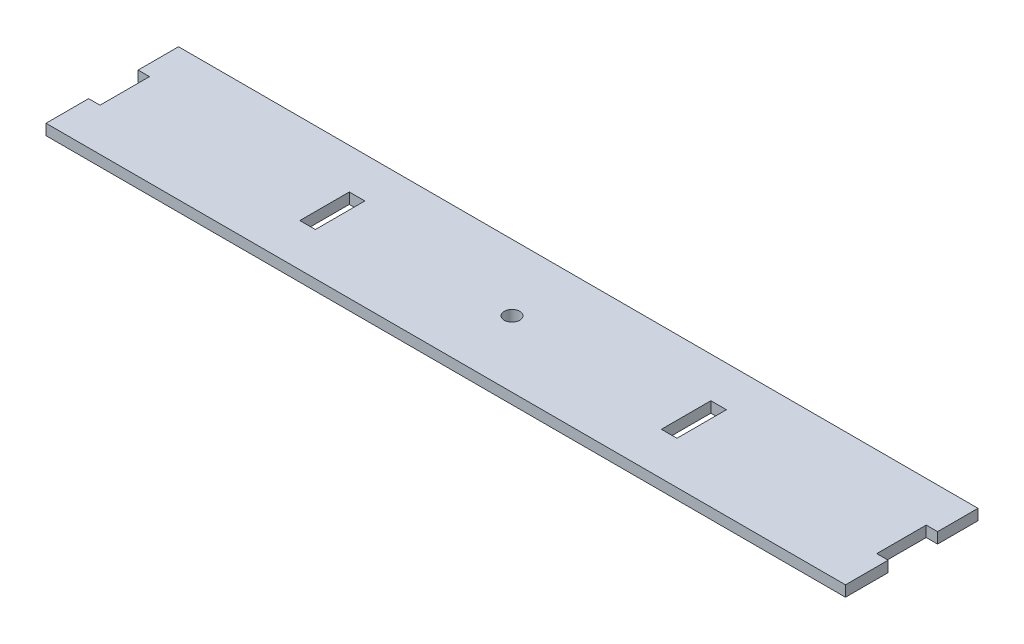
SolidWorks part; units mm, degrees
material "Plain Carbon Steel"
ref_plane "Front Plane" through (0, 0, 0) normal (0, 0, 1) x (1, 0, 0)
ref_plane "Top Plane" through (0, 0, 0) normal (0, 1, 0) x (1, 0, 0)
ref_plane "Right Plane" through (0, 0, 0) normal (1, 0, 0) x (0, 0, -1)
sketch "Sketch1" plane through (0, 0, 0) normal (0, 1, 0) x (1, 0, 0)
  line L0 (0, 29.21) -> (0, 0) construction
  line L1 (-177.8, 29.21) -> (177.8, 29.21)
  line L2 (-177.8, 29.21) -> (-177.8, -29.21)
  line L3 (-177.8, -29.21) -> (177.8, -29.21)
  line L4 (177.8, 29.21) -> (177.8, -29.21)
  line L5 (0, 0) -> (177.8, 0) construction
  dimension "D1" = 177.8
  dimension "D2" = 29.21
extrude "Boss-Extrude1" add sketch "Sketch1" along normal blind 4.7625
sketch "Sketch2" plane through (0, 0, 0) normal (0, -1, 0) x (-1, 0, 0)
  line L0 (177.8, 29.21) -> (177.8, -29.21) construction
  line L1 (171.45, -10.16) -> (177.8, -10.16)
  line L2 (171.45, -10.16) -> (171.45, 11.1389)
  line L3 (171.45, 11.1389) -> (177.8, 11.1389)
  line L4 (177.8, -10.16) -> (177.8, 11.1389)
  line L5 (171.45, 11.1389) -> (177.8, 11.1389) construction
  line L6 (-177.8, -29.21) -> (-177.8, 29.21) construction
  line L7 (82.55, -10.16) -> (76.2, -10.16)
  line L8 (82.55, -10.16) -> (82.55, 11.1389)
  line L9 (82.55, 11.1389) -> (76.2, 11.1389)
  line L10 (76.2, -10.16) -> (76.2, 11.1389)
  line L11 (-76.2, -10.16) -> (-82.55, -10.16)
  line L12 (-76.2, -10.16) -> (-76.2, 11.1389)
  line L13 (-76.2, 11.1389) -> (-82.55, 11.1389)
  line L14 (-82.55, -10.16) -> (-82.55, 11.1389)
  line L15 (-171.45, -10.16) -> (-177.8, -10.16)
  line L16 (-171.45, -10.16) -> (-171.45, 11.1389)
  line L17 (-171.45, 11.1389) -> (-177.8, 11.1389)
  line L18 (-177.8, -10.16) -> (-177.8, 11.1389)
  line L19 (-177.8, 11.1389) -> (-171.45, 11.1389) construction
  line L20 (171.196, -10.414) -> (171.196, 11.3929)
  line L21 (171.196, 11.3929) -> (178.054, 11.3929)
  line L22 (178.054, -10.414) -> (178.054, 11.3929)
  line L23 (171.196, -10.414) -> (178.054, -10.414)
  line L24 (75.946, -10.414) -> (75.946, 11.3929)
  line L25 (82.804, 11.3929) -> (75.946, 11.3929)
  line L26 (82.804, -10.414) -> (82.804, 11.3929)
  line L27 (82.804, -10.414) -> (75.946, -10.414)
  line L28 (-82.804, -10.414) -> (-82.804, 11.3929)
  line L29 (-75.946, 11.3929) -> (-82.804, 11.3929)
  line L30 (-75.946, -10.414) -> (-75.946, 11.3929)
  line L31 (-75.946, -10.414) -> (-82.804, -10.414)
  line L32 (-171.196, -10.414) -> (-171.196, 11.3929)
  line L33 (-171.196, 11.3929) -> (-178.054, 11.3929)
  line L34 (-178.054, -10.414) -> (-178.054, 11.3929)
  line L35 (-171.196, -10.414) -> (-178.054, -10.414)
  dimension "D1" = 0.254
extrude "Cut-Extrude1" cut sketch "Sketch2" against normal through all
sketch "Sketch3" plane through (0, 0, 0) normal (0, -1, 0) x (1, 0, 0)
  line L0 (176.2125, -29.21) -> (176.2125, 29.21)
  line L1 (-176.2125, 29.21) -> (-176.2125, -29.21)
  line L12 (171.196, -11.3929) -> (171.196, 10.414)
  line L13 (171.196, 10.414) -> (177.8, 10.414)
  line L14 (177.8, 10.414) -> (177.8, 29.21)
  line L15 (177.8, 29.21) -> (-177.8, 29.21)
  line L16 (-177.8, 29.21) -> (-177.8, 10.414)
  line L17 (-177.8, 10.414) -> (-171.196, 10.414)
  line L18 (-171.196, 10.414) -> (-171.196, -11.3929)
  line L19 (-171.196, -11.3929) -> (-177.8, -11.3929)
  line L20 (-177.8, -11.3929) -> (-177.8, -29.21)
  line L21 (-177.8, -29.21) -> (177.8, -29.21)
  line L22 (177.8, -29.21) -> (177.8, -11.3929)
  line L23 (177.8, -11.3929) -> (171.196, -11.3929)
  line L24 (171.196, -11.3929) -> (171.196, 10.414)
  line L25 (171.196, 10.414) -> (177.8, 10.414)
  line L26 (177.8, 10.414) -> (177.8, 29.21)
  line L27 (177.8, 29.21) -> (-177.8, 29.21)
  line L28 (-177.8, 29.21) -> (-177.8, 10.414)
  line L29 (-177.8, 10.414) -> (-171.196, 10.414)
  line L30 (-171.196, 10.414) -> (-171.196, -11.3929)
  line L31 (-171.196, -11.3929) -> (-177.8, -11.3929)
  line L32 (-177.8, -11.3929) -> (-177.8, -29.21)
  line L33 (-177.8, -29.21) -> (177.8, -29.21)
  line L34 (177.8, -29.21) -> (177.8, -11.3929)
  line L35 (177.8, -11.3929) -> (171.196, -11.3929)
  line M22 (171.196, 10.414) -> (177.8, 10.414)
  line M23 (177.8, 10.414) -> (177.8, 29.21)
  line M24 (177.8, 29.21) -> (-177.8, 29.21)
  line M25 (-177.8, 29.21) -> (-177.8, 10.414)
  line M26 (-177.8, 10.414) -> (-171.196, 10.414)
  line M28 (-171.196, -11.3929) -> (-177.8, -11.3929)
  line M29 (-177.8, -11.3929) -> (-177.8, -29.21)
  line M30 (-177.8, -29.21) -> (177.8, -29.21)
  line M31 (177.8, -29.21) -> (177.8, -11.3929)
  line M32 (177.8, -11.3929) -> (171.196, -11.3929)
  dimension "D2" = 1.5875
  dimension "D3" = 1.5875
  dimension "D1" = 0
extrude "Cut-Extrude2" cut sketch "Sketch3" against normal through all contours L0 M30 M31 M32 | L0 M22 M23 M24 | L1 M28 M29 M30 | L1 M24 M25 M26
sketch "Sketch4" plane through (0, 0, 0) normal (0, -1, 0) x (1, 0, 0)
  line L0 (-75.946, 10.414) -> (-82.804, 10.414) construction
  line L1 (75.946, -11.3929) -> (76.2635, -11.3929)
  line L2 (75.946, -11.3929) -> (75.946, 10.414)
  line L3 (75.946, 10.414) -> (76.2635, 10.414)
  line L4 (76.2635, -11.3929) -> (76.2635, 10.414)
  line L5 (-75.946, -11.3929) -> (-76.2635, -11.3929)
  line L6 (-75.946, -11.3929) -> (-75.946, 10.414)
  line L7 (-75.946, 10.414) -> (-76.2635, 10.414)
  line L8 (-76.2635, -11.3929) -> (-76.2635, 10.414)
  dimension "D1" = 152.527
extrude "Boss-Extrude2" add sketch "Sketch4" against normal up to surface (4.7625 mm away) up to face at (79.375, 4.7625, -0.4895)
sketch "Sketch5" plane through (0, 0, 0) normal (0, -1, 0) x (1, 0, 0)
  line L0 (-76.2635, 10.414) -> (-82.804, 10.414) construction
  line L1 (-82.804, -11.3929) -> (-83.1215, -11.3929)
  line L2 (-82.804, -11.3929) -> (-82.804, 10.414)
  line L3 (-82.804, 10.414) -> (-83.1215, 10.414)
  line L4 (-83.1215, -11.3929) -> (-83.1215, 10.414)
  line L5 (82.804, -11.3929) -> (83.1215, -11.3929)
  line L6 (82.804, -11.3929) -> (82.804, 10.414)
  line L7 (82.804, 10.414) -> (83.1215, 10.414)
  line L8 (83.1215, -11.3929) -> (83.1215, 10.414)
  line L9 (-76.2635, 10.414) -> (-76.2635, -11.3929) construction
  dimension "D1" = 6.858
extrude "Cut-Extrude3" cut sketch "Sketch5" against normal through all
sketch "Sketch6" plane through (0, 0, 0) normal (0, -1, 0) x (1, 0, 0)
  line L0 (0, 29.21) -> (0, -29.21) construction
  line L1 (176.2125, -29.21) -> (-176.2125, -29.21) construction
  circle A0 centre (0, 0) radius 3.429
extrude "Cut-Extrude4" cut sketch "Sketch6" against normal through all
